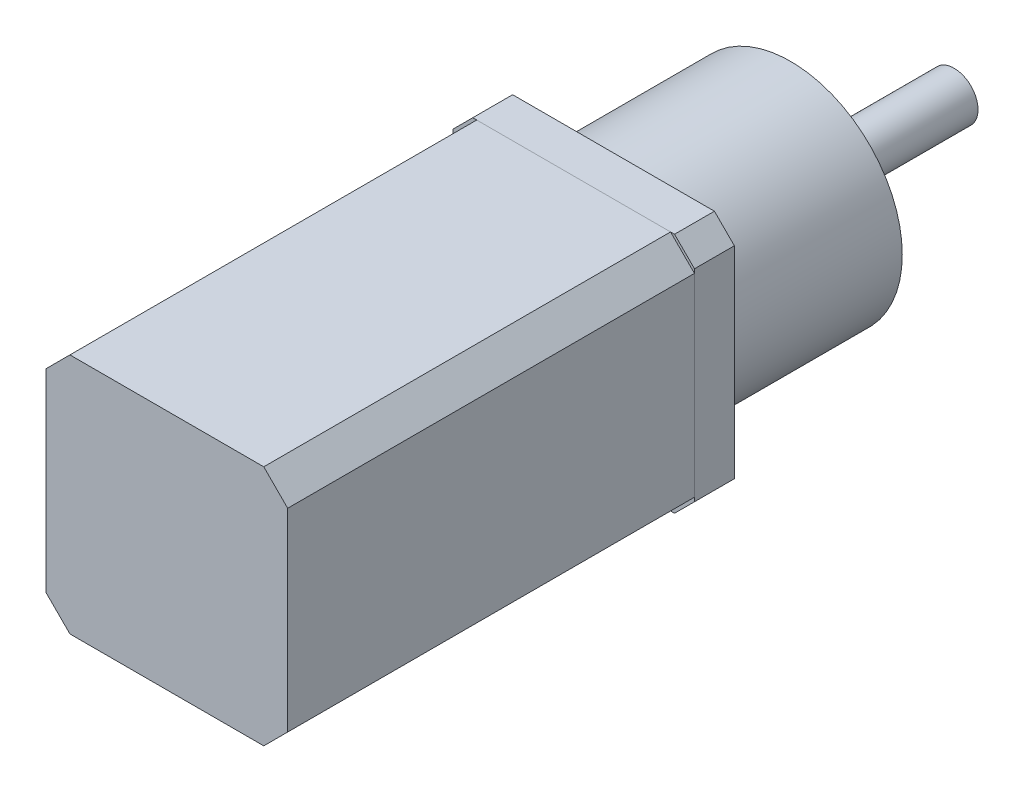
SolidWorks part; units mm, degrees
ref_plane "Front Plane" through (0, 0, 0) normal (0, 0, 1) x (1, 0, 0)
ref_plane "Top Plane" through (0, 0, 0) normal (0, 1, 0) x (1, 0, 0)
ref_plane "Right Plane" through (0, 0, 0) normal (1, 0, 0) x (0, 0, -1)
sketch "Sketch1" plane through (0, 0, 0) normal (0, 0, 1) x (1, 0, 0)
  line L1 (-15.15, 15.15) -> (15.15, 15.15)
  line L2 (-15.15, 15.15) -> (-15.15, -15.15)
  line L3 (-15.15, -15.15) -> (15.15, -15.15)
  line L4 (15.15, 15.15) -> (15.15, -15.15)
  line L5 (-15.15, 15.15) -> (15.15, -15.15) construction
  line L6 (-15.15, -15.15) -> (15.15, 15.15) construction
  point P0 (0, 0)
  dimension "D1" = 30.3
  dimension "D2" = 30.3
extrude "Boss-Extrude1" add sketch "Sketch1" along normal blind 51
sketch "Sketch4" plane through (0, 0, 0) normal (0, 0, -1) x (-1, 0, 0)
  line L1 (-15.15, -15.15) -> (15.15, -15.15)
  line L2 (-15.15, -15.15) -> (-15.15, 15.15)
  line L3 (-15.15, 15.15) -> (15.15, 15.15)
  line L4 (15.15, -15.15) -> (15.15, 15.15)
  line L5 (-15.15, -15.15) -> (15.15, 15.15) construction
  line L6 (-15.15, 15.15) -> (15.15, -15.15) construction
  point P0 (0, 0)
extrude "Boss-Extrude4" add sketch "Sketch4" along normal blind 5 separate body
sketch "Sketch5" plane through (0, 0, -5) normal (0, 0, -1) x (-1, 0, 0)
  circle A0 centre (0, 0) radius 14
  dimension "D1" = 28
extrude "Boss-Extrude5" add sketch "Sketch5" along normal blind 22.2
sketch "Sketch6" plane through (0, 0, -27.2) normal (0, 0, -1) x (-1, 0, 0)
  circle A0 centre (0, 0) radius 9
  dimension "D1" = 18
extrude "Boss-Extrude6" add sketch "Sketch6" along normal blind 2
sketch "Sketch7" plane through (0, 0, -29.2) normal (0, 0, -1) x (-1, 0, 0)
  circle A0 centre (0, 0) radius 3
  dimension "D1" = 6
extrude "Boss-Extrude7" add sketch "Sketch7" along normal blind 18.5
sketch "Sketch8" plane through (0, 0, -29.2) normal (0, 0, -1) x (-1, 0, 0)
  circle A0 centre (0, 0) radius 4.3223
extrude "Boss-Extrude8" add sketch "Sketch8" along normal blind 0.4
chamfer "Chamfer1" distance 3 angle 45 4 edges at (-15.15, -15.15, 25.5) (15.15, -15.15, 25.5) (-15.15, 15.15, 25.5) (15.15, 15.15, 25.5)
chamfer "Chamfer2" distance 2.5 angle 45 4 edges at (15.15, 15.15, -2.5) (15.15, -15.15, -2.5) (-15.15, -15.15, -2.5) (-15.15, 15.15, -2.5)
